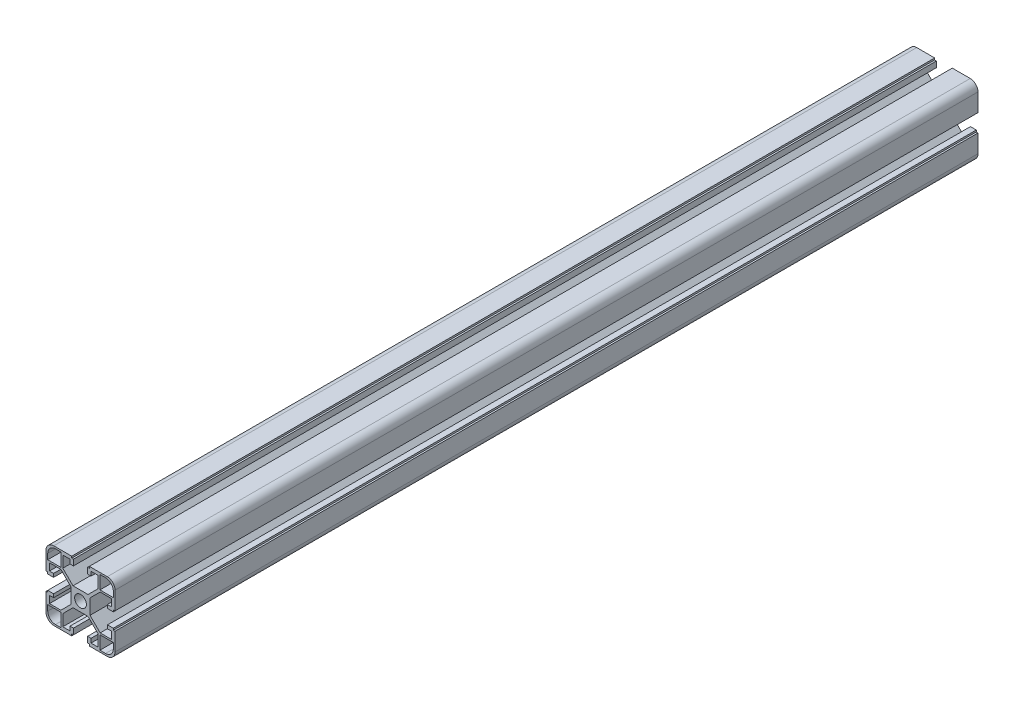
SolidWorks part; units mm, degrees
material "6061 合金"
ref_plane "前视基准面" through (0, 0, 0) normal (0, 0, 1) x (1, 0, 0)
ref_plane "上视基准面" through (0, 0, 0) normal (0, 1, 0) x (1, 0, 0)
ref_plane "右视基准面" through (0, 0, 0) normal (1, 0, 0) x (0, 0, -1)
other "Configuration Table"
sketch "草图1" plane through (0, 0, 0) normal (0, 0, 1) x (1, 0, 0)
  line L1 (-20, 20) -> (20, 20)
  line L2 (-20, 20) -> (-20, -20)
  line L3 (-20, -20) -> (20, -20)
  line L4 (20, 20) -> (20, -20)
  line L5 (-20, 20) -> (20, -20) construction
  line L6 (-20, -20) -> (20, 20) construction
  point P0 (0, 0)
  dimension "D1" = 40
  dimension "D2" = 40
extrude "凸台-拉伸1" add sketch "草图1" against normal blind 500
sketch "草图2" plane through (0, 0, 0) normal (0, 0, 1) x (1, 0, 0)
  line L0 (0, 0) -> (-20, 0) construction
  line L1 (-20, 20) -> (-20, -20) construction
  line L2 (-20, 5.1) -> (-19, 5.1)
  line L3 (-19, 5.1) -> (-19, 4.1)
  line L4 (-19, 4.1) -> (-15.6, 4.1)
  line L5 (-15.6, 4.1) -> (-15.6, 6.1)
  line L6 (-15.6, 6.1) -> (-18, 6.1)
  line L7 (-18, 6.1) -> (-18, 10.25)
  line L8 (-18, 10.25) -> (-11.3814, 10.25)
  line L9 (-11.3814, 10.25) -> (-5.5, 4.3686)
  line L10 (-11.3814, -10.25) -> (-5.5, -4.3686)
  line L11 (-5.5, 5.5) -> (5.5, 5.5)
  line L12 (-5.5, 5.5) -> (-5.5, -5.5)
  line L13 (-5.5, -5.5) -> (5.5, -5.5)
  line L14 (5.5, 5.5) -> (5.5, -5.5)
  line L15 (-5.5, 5.5) -> (5.5, -5.5) construction
  line L16 (-5.5, -5.5) -> (5.5, 5.5) construction
  line L17 (-18, -10.25) -> (-11.3814, -10.25)
  line L18 (-18, -6.1) -> (-18, -10.25)
  line L19 (-15.6, -6.1) -> (-18, -6.1)
  line L20 (-15.6, -4.1) -> (-15.6, -6.1)
  line L21 (-19, -4.1) -> (-15.6, -4.1)
  line L22 (-19, -5.1) -> (-19, -4.1)
  line L23 (-20, -5.1) -> (-19, -5.1)
  line L24 (-20, 5.1) -> (-20, -5.1)
  line L25 (5.1, 20) -> (5.1, 19)
  line L26 (5.1, 19) -> (4.1, 19)
  line L27 (4.1, 19) -> (4.1, 15.6)
  line L28 (4.1, 15.6) -> (6.1, 15.6)
  line L29 (6.1, 15.6) -> (6.1, 18)
  line L30 (6.1, 18) -> (10.25, 18)
  line L31 (10.25, 18) -> (10.25, 11.3814)
  line L32 (10.25, 11.3814) -> (4.3686, 5.5)
  line L33 (-10.25, 11.3814) -> (-4.3686, 5.5)
  line L34 (-10.25, 18) -> (-10.25, 11.3814)
  line L35 (-6.1, 18) -> (-10.25, 18)
  line L36 (-6.1, 15.6) -> (-6.1, 18)
  line L37 (-4.1, 15.6) -> (-6.1, 15.6)
  line L38 (-4.1, 19) -> (-4.1, 15.6)
  line L39 (-5.1, 19) -> (-4.1, 19)
  line L40 (-5.1, 20) -> (-5.1, 19)
  line L41 (5.1, 20) -> (-5.1, 20)
  line L42 (0, 0) -> (0, 20) construction
  line L43 (20, -5.1) -> (19, -5.1)
  line L44 (19, -5.1) -> (19, -4.1)
  line L45 (19, -4.1) -> (15.6, -4.1)
  line L46 (15.6, -4.1) -> (15.6, -6.1)
  line L47 (15.6, -6.1) -> (18, -6.1)
  line L48 (18, -6.1) -> (18, -10.25)
  line L49 (18, -10.25) -> (11.3814, -10.25)
  line L50 (11.3814, -10.25) -> (5.5, -4.3686)
  line L51 (11.3814, 10.25) -> (5.5, 4.3686)
  line L52 (18, 10.25) -> (11.3814, 10.25)
  line L53 (18, 6.1) -> (18, 10.25)
  line L54 (15.6, 6.1) -> (18, 6.1)
  line L55 (15.6, 4.1) -> (15.6, 6.1)
  line L56 (19, 4.1) -> (15.6, 4.1)
  line L57 (19, 5.1) -> (19, 4.1)
  line L58 (20, 5.1) -> (19, 5.1)
  line L59 (20, -5.1) -> (20, 5.1)
  line L60 (0, 0) -> (20, 0) construction
  line L61 (-5.1, -20) -> (-5.1, -19)
  line L62 (-5.1, -19) -> (-4.1, -19)
  line L63 (-4.1, -19) -> (-4.1, -15.6)
  line L64 (-4.1, -15.6) -> (-6.1, -15.6)
  line L65 (-6.1, -15.6) -> (-6.1, -18)
  line L66 (-6.1, -18) -> (-10.25, -18)
  line L67 (-10.25, -18) -> (-10.25, -11.3814)
  line L68 (-10.25, -11.3814) -> (-4.3686, -5.5)
  line L69 (10.25, -11.3814) -> (4.3686, -5.5)
  line L70 (10.25, -18) -> (10.25, -11.3814)
  line L71 (6.1, -18) -> (10.25, -18)
  line L72 (6.1, -15.6) -> (6.1, -18)
  line L73 (4.1, -15.6) -> (6.1, -15.6)
  line L74 (4.1, -19) -> (4.1, -15.6)
  line L75 (5.1, -19) -> (4.1, -19)
  line L76 (5.1, -20) -> (5.1, -19)
  line L77 (-5.1, -20) -> (5.1, -20)
  line L78 (0, 0) -> (0, -20) construction
  point P18 (4.1, 15.6)
  point P28 (3.2964, 5.5)
  point P29 (0, 0)
  point P87 (0, 0)
  point P88 (15.6, -4.1)
  line M77 (20, -20) -> (20, 20)
  line M78 (20, 20) -> (-20, 20)
  line M79 (-20, 20) -> (-20, -20)
  line M80 (-20, -20) -> (20, -20)
  dimension "D1" = 11
  dimension "D2" = 11
  dimension "D3" = 8.2
  dimension "D4" = 10.1
  dimension "D5" = 1
  dimension "D7" = 1.6
  dimension "D8" = 1
  dimension "D9" = 20.5
  dimension "D10" = 2
  dimension "D11" = 2
  dimension "D6" = 4
extrude "切除-拉伸1" cut sketch "草图2" against normal through all contours L23 L22 L21 L20 L19 L18 L17 L10 L12 L9 L8 L7 L6 L5 L4 L3 L2 M79 | L76 L75 L74 L73 L72 L71 L70 L69 L13 L68 L67 L66 L65 L64 L63 L62 L61 M80 | L58 L57 L56 L55 L54 L53 L52 L51 L14 L50 L49 L48 L47 L46 L45 L44 L43 M77 | L40 L39 L38 L37 L36 L35 L34 L33 L11 L32 L31 L30 L29 L28 L27 L26 L25 M78
sketch "草图3" plane through (0, 0, 0) normal (0, 0, 1) x (1, 0, 0)
  line L0 (-10.25, 18) -> (-10.25, 11.3814) construction
  line L1 (-19, 19) -> (-11.25, 19)
  line L2 (-19, 19) -> (-19, 11.25)
  line L3 (-19, 11.25) -> (-11.25, 11.25)
  line L4 (-11.25, 19) -> (-11.25, 11.25)
  line L5 (-19, 19) -> (-11.25, 11.25) construction
  line L6 (-19, 11.25) -> (-11.25, 19) construction
  line L7 (-18, 10.25) -> (-11.3814, 10.25) construction
  line L8 (-20, 20) -> (-20, 5.1) construction
  line L9 (-5.1, 20) -> (-20, 20) construction
  line L10 (19, 19) -> (19, 11.25)
  line L11 (19, 19) -> (11.25, 19)
  line L12 (11.25, 19) -> (11.25, 11.25)
  line L13 (19, 11.25) -> (11.25, 11.25)
  line L14 (19, 19) -> (11.25, 11.25) construction
  line L15 (11.25, 19) -> (19, 11.25) construction
  line L16 (19, -19) -> (11.25, -19)
  line L17 (19, -19) -> (19, -11.25)
  line L18 (19, -11.25) -> (11.25, -11.25)
  line L19 (11.25, -19) -> (11.25, -11.25)
  line L20 (19, -19) -> (11.25, -11.25) construction
  line L21 (19, -11.25) -> (11.25, -19) construction
  line L22 (-19, -19) -> (-19, -11.25)
  line L23 (-19, -19) -> (-11.25, -19)
  line L24 (-11.25, -19) -> (-11.25, -11.25)
  line L25 (-19, -11.25) -> (-11.25, -11.25)
  line L26 (-19, -19) -> (-11.25, -11.25) construction
  line L27 (-11.25, -19) -> (-19, -11.25) construction
  point P0 (-15.125, 15.125)
  point P13 (18.2024, 14.434)
  point P14 (0, 0)
  point P16 (15.125, 15.125)
  point P21 (15.125, -15.125)
  point P26 (-15.125, -15.125)
  point P31 (0, 0)
  dimension "D1" = 1
  dimension "D2" = 1
  dimension "D3" = 1
  dimension "D4" = 1
  dimension "D5" = 4
extrude "切除-拉伸2" cut sketch "草图3" against normal through all
sketch "草图4" plane through (0, 0, 0) normal (0, 0, 1) x (1, 0, 0)
  circle A0 centre (0, 0) radius 3.4
  dimension "D1" = 6.8
extrude "切除-拉伸3" cut sketch "草图4" against normal through all
fillet "圆角1" radius 4.5 8 edges at (-20, 20, -250) (-19, 19, -250) (19, 19, -250) (20, 20, -250) (20, -20, -250) (19, -19, -250) (-20, -20, -250) (-19, -19, -250)
equation "\"length\"= 500"
